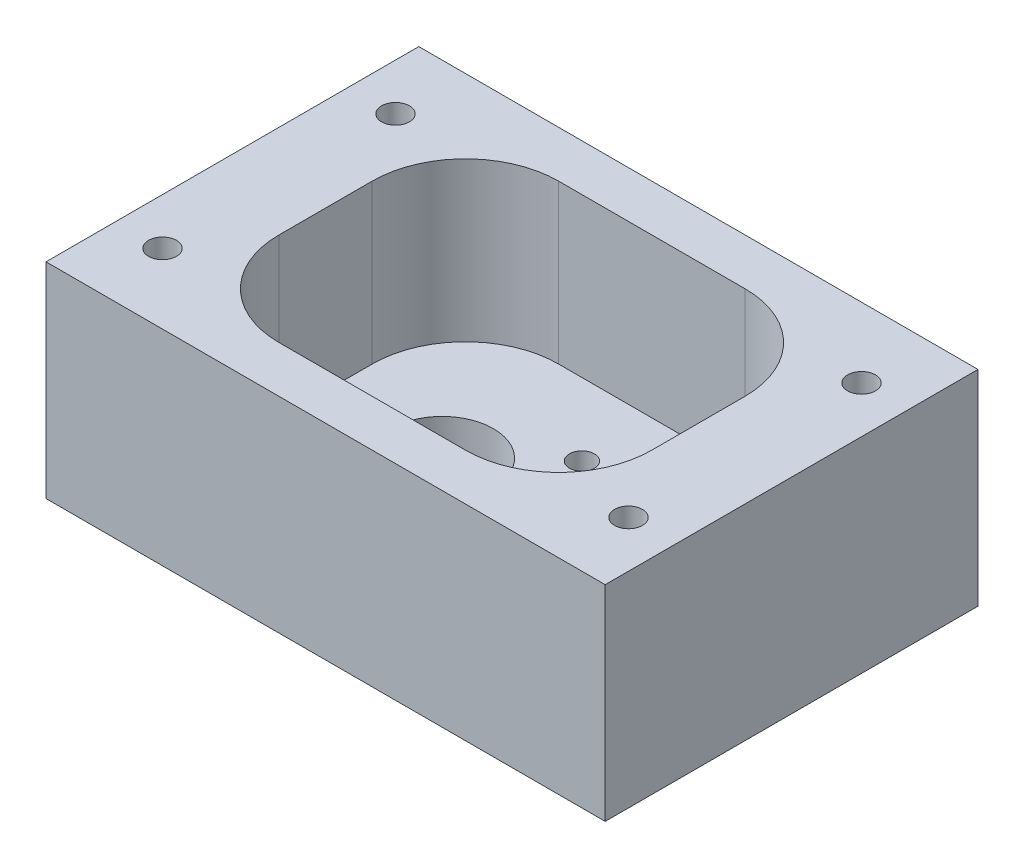
SolidWorks part; units mm, degrees
material "6061 Alloy"
ref_plane "Front Plane" through (0, 0, 0) normal (0, 0, 1) x (1, 0, 0)
ref_plane "Top Plane" through (0, 0, 0) normal (0, 1, 0) x (1, 0, 0)
ref_plane "Right Plane" through (0, 0, 0) normal (1, 0, 0) x (0, 0, -1)
sketch "Sketch1" plane through (0, 0, 0) normal (0, 1, 0) x (1, 0, 0)
  line L1 (-38.1, -25.4) -> (38.1, -25.4)
  line L2 (-38.1, -25.4) -> (-38.1, 25.4)
  line L3 (-38.1, 25.4) -> (38.1, 25.4)
  line L4 (38.1, -25.4) -> (38.1, 25.4)
  line L5 (-38.1, -25.4) -> (38.1, 25.4) construction
  line L6 (-38.1, 25.4) -> (38.1, -25.4) construction
  point P0 (0, 0)
  dimension "D1" = 76.2
  dimension "D2" = 50.8
extrude "Boss-Extrude1" add sketch "Sketch1" along normal blind 27.94
sketch "Sketch2" plane through (0, 0, 0) normal (0, -1, 0) x (1, 0, 0)
  line L0 (-38.1, 0) -> (38.1, 0) construction
  line L1 (-38.1, -25.4) -> (-38.1, 25.4) construction
  line L2 (38.1, 25.4) -> (38.1, -25.4) construction
  line L3 (0, 25.4) -> (0, -25.4) construction
  line L4 (-38.1, 25.4) -> (38.1, 25.4) construction
  line L5 (38.1, -25.4) -> (-38.1, -25.4) construction
  circle A0 centre (-9.525, 0) radius 6.985
  circle A1 centre (9.525, 0) radius 9
  point P12 (-9.525, 0)
  point P13 (9.525, 0)
  dimension "D3" = 18
  dimension "D4" = 13.97
  dimension "D1" = 19.05
  dimension "D2" = 9.525
extrude "Cut-Extrude1" cut sketch "Sketch2" against normal through all contours A0 | A1
sketch "Sketch3" plane through (0, 27.94, 0) normal (0, 1, 0) x (1, 0, 0)
  line L0 (9.525, 0) -> (-9.525, 0) construction
  line L1 (-12.7, -19.05) -> (12.7, -19.05)
  line L2 (-25.4, -6.35) -> (-25.4, 6.35)
  line L3 (-12.7, 19.05) -> (12.7, 19.05)
  line L4 (25.4, -6.35) -> (25.4, 6.35)
  line L5 (-25.4, -19.05) -> (25.4, 19.05) construction
  line L6 (-25.4, 19.05) -> (25.4, -19.05) construction
  arc A0 (12.7, 19.05) -> (25.4, 6.35) centre (12.7, 6.35) cw
  arc A1 (25.4, -6.35) -> (12.7, -19.05) centre (12.7, -6.35) cw
  arc A2 (-12.7, -19.05) -> (-25.4, -6.35) centre (-12.7, -6.35) cw
  arc A3 (-25.4, 6.35) -> (-12.7, 19.05) centre (-12.7, 6.35) cw
  point P0 (0, 0)
  dimension "D3" = 12.7
  dimension "D1" = 38.1
  dimension "D2" = 50.8
extrude "Cut-Extrude2" cut sketch "Sketch3" against normal blind 21.59
sketch "Sketch4" plane through (0, 0, 0) normal (0, -1, 0) x (1, 0, 0)
  line L0 (-31.75, 25.4) -> (-31.75, -25.4) construction
  line L1 (-38.1, 25.4) -> (38.1, 25.4) construction
  line L2 (38.1, -25.4) -> (-38.1, -25.4) construction
  line L3 (31.75, 25.4) -> (31.75, -25.4) construction
  line L4 (-38.1, -25.4) -> (-38.1, 25.4) construction
  line L5 (38.1, 25.4) -> (38.1, -25.4) construction
  line L6 (-31.75, 0) -> (31.75, 0) construction
  line L7 (0.3326, 9.1924) -> (18.7174, -9.1924) construction
  line L8 (18.7174, 9.1924) -> (0.3326, -9.1924) construction
  circle A1 centre (9.525, 0) radius 9 construction
  point P12 (-31.75, 15.875)
  point P13 (-31.75, -15.875)
  point P14 (31.75, 15.875)
  point P15 (31.75, -15.875)
  point P20 (9.525, 0)
  point P25 (9.525, 0)
  point P27 (0.3326, 9.1924)
  point P28 (18.7174, 9.1924)
  point P29 (18.7174, -9.1924)
  point P30 (0.3326, -9.1924)
  dimension "D1" = 6.35
  dimension "D2" = 6.35
  dimension "D3" = 31.75
  dimension "D4" = 45
  dimension "D5" = 45
  dimension "D6" = 26
hole_wizard "M3 Clearance Hole1" positions "3DSketch1" profile "Sketch5" hole size "M3" standard "ANSI Metric" end condition through all
sketch3d "3DSketch1"
  point P6 (0.3326, 0, 9.1924)
  point P9 (0.3326, 0, -9.1924)
  point P12 (18.7174, 0, 9.1924)
  point P15 (18.7174, 0, -9.1924)
  point P25 (0, 0, 0)
sketch "Sketch5" plane through (0.3326, 0, 9.1924) normal (1, 0, 0) x (0, 0, -1)
  line L0 (0, 0) -> (0, 27.94)
  line L1 (0, 27.94) -> (1.7, 27.94)
  line L2 (1.7, 27.94) -> (1.7, 0)
  line L5 (1.7, 0) -> (0, 0)
  line L11 (0, -6.35) -> (0, 107.95) construction
  dimension "Thru Hole Dia." = 3.4
  dimension "Thru Hole Depth" = 27.94
hole_wizard "#6 Clearance Hole1" positions "3DSketch2" profile "Sketch6" hole size "#6" standard "ANSI Inch" end condition through all
sketch3d "3DSketch2"
  point P0 (-31.75, 0, 15.875)
  point P3 (-31.75, 0, -15.875)
  point P6 (31.75, 0, 15.875)
  point P9 (31.75, 0, -15.875)
sketch "Sketch6" plane through (-31.75, 0, 15.875) normal (1, 0, 0) x (0, 0, -1)
  line L0 (0, 0) -> (0, 27.94)
  line L1 (0, 27.94) -> (1.8986, 27.94)
  line L2 (1.8986, 27.94) -> (1.8986, 0)
  line L5 (1.8986, 0) -> (0, 0)
  line L11 (0, -6.35) -> (0, 107.95) construction
  dimension "Thru Hole Dia." = 3.7973
  dimension "Thru Hole Depth" = 27.94
equation "\"D2@Sketch4\"=\"D1@Sketch4\""
equation "\"D2@Sketch2\"=\"D1@Sketch2\"/2"
